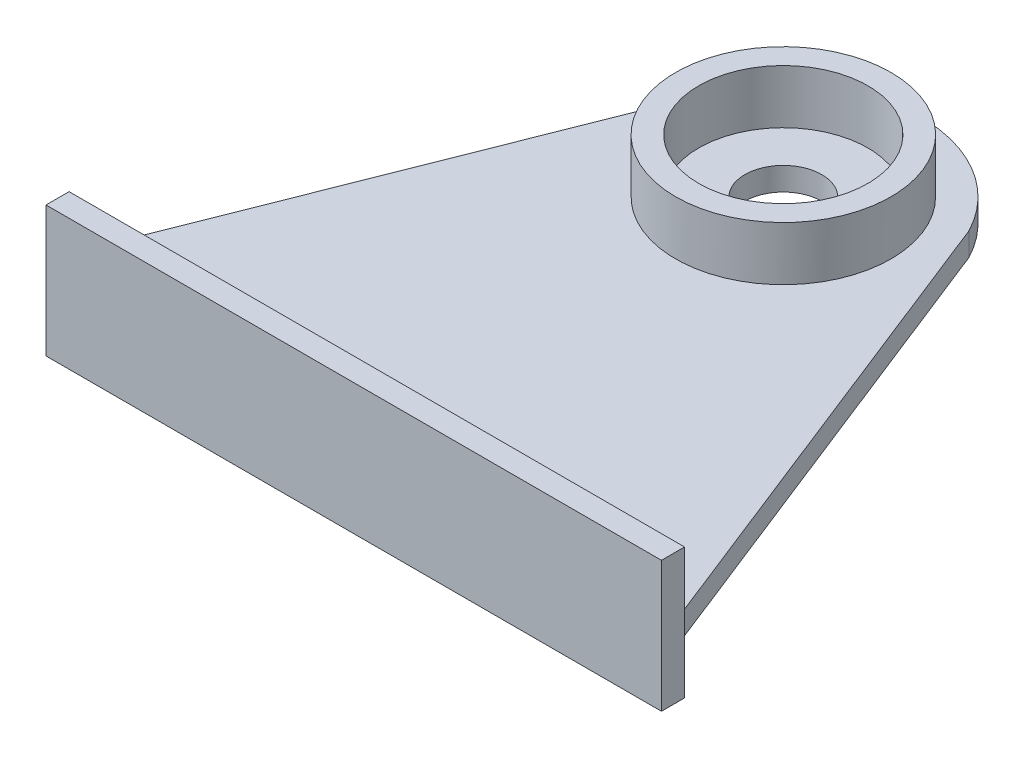
SolidWorks part; units mm, degrees
ref_plane "Front Plane" through (0, 0, 0) normal (0, 0, 1) x (1, 0, 0)
ref_plane "Top Plane" through (0, 0, 0) normal (0, 1, 0) x (1, 0, 0)
ref_plane "Right Plane" through (0, 0, 0) normal (1, 0, 0) x (0, 0, -1)
sketch "Sketch1" plane through (0, 0, 0) normal (0, 1, 0) x (1, 0, 0)
  line L0 (-48.9291, -17.8351) -> (31.0709, -17.8351)
  line L1 (31.0709, -17.8351) -> (6.9855, 43.197)
  line L2 (-24.8438, 43.197) -> (-48.9291, -17.8351)
  line L3 (-8.9291, -17.8351) -> (-8.9291, 35.0049) construction
  arc A0 (-24.8438, 43.197) -> (6.9855, 43.197) centre (-8.9291, 35.0049) cw
  circle A1 centre (-8.9291, 35.0049) radius 11 construction
  dimension "D3" = 22
  dimension "D1" = 80
  dimension "D4" = 52.84
extrude "Boss-Extrude1" add sketch "Sketch1" along normal blind 3
sketch "Sketch2" plane through (0, 3, 0) normal (0, 1, 0) x (1, 0, 0)
  circle A0 centre (-8.9291, 35.0049) radius 11
  circle A1 centre (-8.9291, 35.0049) radius 14
  dimension "D1" = 28
  dimension "D2" = 22
extrude "Boss-Extrude2" add sketch "Sketch2" along normal blind 7
sketch "Sketch3" plane through (0, 0, 17.8351) normal (0, 0, 1) x (1, 0, 0)
  line L0 (-48.9291, 3) -> (-48.9291, 0) construction
  line L1 (-48.9291, -7) -> (31.0709, -7)
  line L2 (-48.9291, -7) -> (-48.9291, 10)
  line L3 (-48.9291, 10) -> (31.0709, 10)
  line L4 (31.0709, -7) -> (31.0709, 10)
  line L5 (31.0709, 3) -> (31.0709, 0) construction
  dimension "D1" = 7
  dimension "D2" = 17
extrude "Boss-Extrude3" add sketch "Sketch3" along normal blind 3
sketch "Sketch4" plane through (0, 0, 17.8351) normal (0, 0, -1) x (-1, 0, 0)
  line L0 (-31.0709, 10) -> (48.9291, 10) construction
  circle A0 centre (-23.299, 6.5) radius 2.5726
  dimension "D2" = 5.1453
  dimension "D1" = 3.5
sketch "Sketch5" plane through (0, 3, 0) normal (0, 1, 0) x (1, 0, 0)
  circle A0 centre (-8.9291, 35.0049) radius 5
  dimension "D1" = 10
extrude "Cut-Extrude1" cut sketch "Sketch5" against normal blind 10
